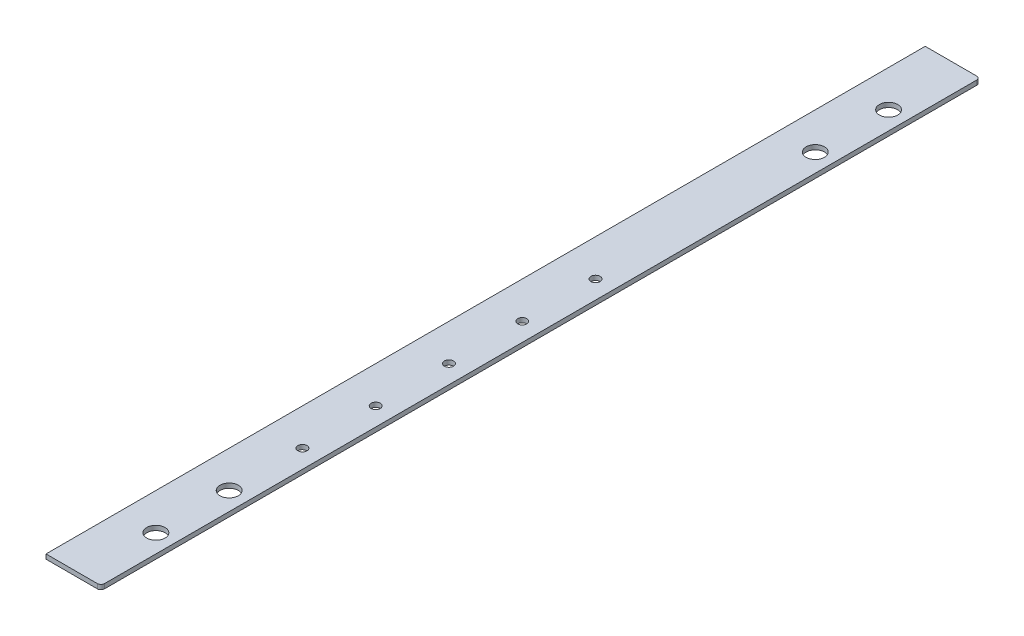
SolidWorks part; units mm, degrees
ref_plane "Front Plane" through (0, 0, 0) normal (0, 0, 1) x (1, 0, 0)
ref_plane "Top Plane" through (0, 0, 0) normal (0, 1, 0) x (1, 0, 0)
ref_plane "Right Plane" through (0, 0, 0) normal (1, 0, 0) x (0, 0, -1)
sketch "Sketch1" plane through (0, 0, 0) normal (0, 1, 0) x (1, 0, 0)
  line L1 (0, 0) -> (38.1, 0)
  line L2 (0, 0) -> (0, 609.6)
  line L3 (0, 609.6) -> (38.1, 609.6)
  line L4 (38.1, 0) -> (38.1, 609.6)
  dimension "D1" = 38.1
  dimension "D2" = 609.6
extrude "Boss-Extrude1" add sketch "Sketch1" along normal blind 3.175
fillet "Fillet1" radius 2.54 2 edges at (38.1, 1.5875, 0) (38.1, 1.5875, -609.6)
sketch "Sketch4" plane through (0, 3.175, 0) normal (0, 1, 0) x (-1, 0, 0)
  line L1 (0, 0) -> (-35.56, 0) construction
  circle A2 centre (-25.4, -152.4) radius 3.175
  circle A3 centre (-25.4, -203.2) radius 3.175
  circle A4 centre (-25.4, -254) radius 3.175
  circle A5 centre (-25.4, -304.8) radius 3.175
  circle A6 centre (-25.4, -355.6) radius 3.175
  circle A7 centre (-25.4, -50.8) radius 6.35
  circle A8 centre (-25.4, -101.6) radius 6.35
  circle A9 centre (-25.4, -558.8) radius 6.35
  circle A10 centre (-25.4, -508) radius 6.35
  dimension "D3" = 50.8
extrude "Cut-Extrude1" cut sketch "Sketch4" against normal through all
